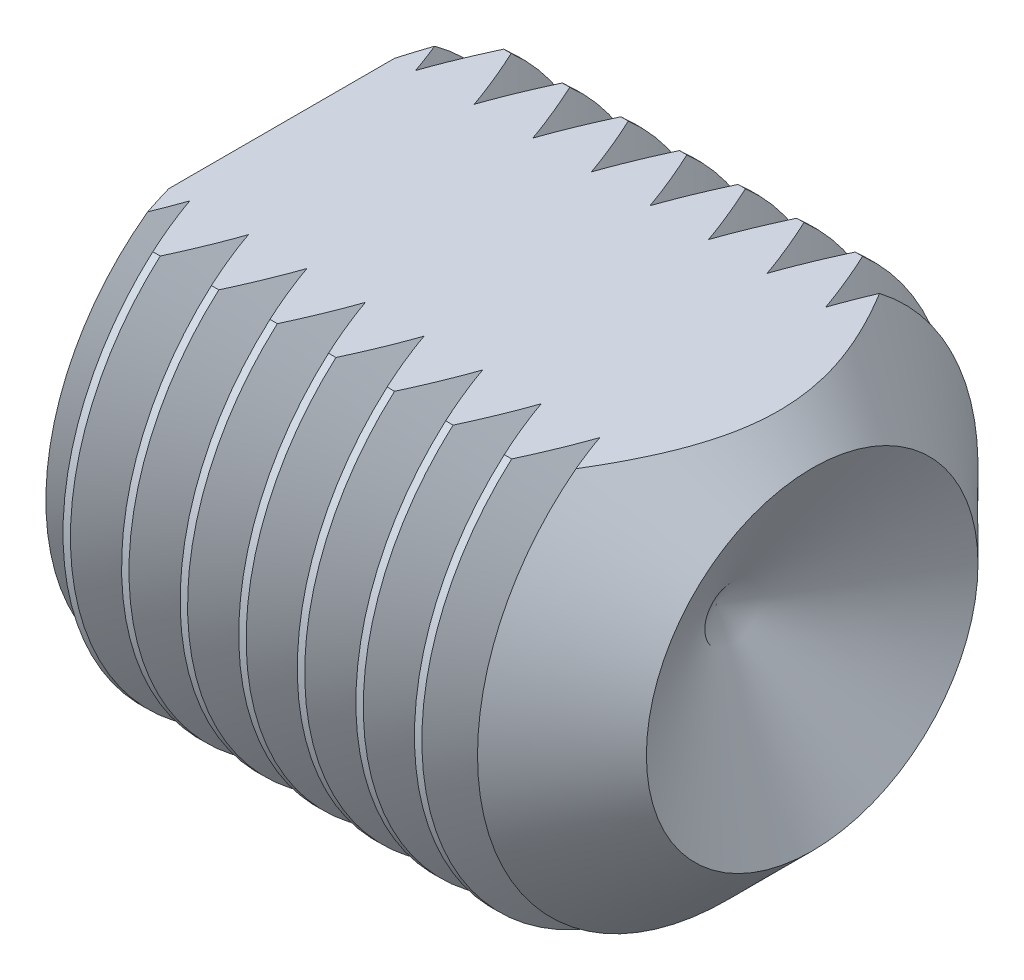
SolidWorks part; units mm, degrees
ref_plane "Plane1" through (0, 0, 0) normal (0, 0, 1) x (1, 0, 0)
ref_plane "Plane2" through (0, 0, 0) normal (0, 1, 0) x (1, 0, 0)
ref_plane "Plane3" through (0, 0, 0) normal (1, 0, 0) x (0, 0, -1)
sketch "BodySke" plane through (0, 0, 0) normal (0, 0, 1) x (1, 0, 0)
  line L0 (0, 0) -> (0, 6.8985)
  line L1 (0, 6.8985) -> (0.636, 8)
  line L2 (0.636, 8) -> (13, 8)
  line L3 (13, 8) -> (16, 5)
  line L4 (13.1132, 0) -> (0, 0)
  line L5 (-12.7, 0) -> (88.9, 0) construction
  line L6 (13.1132, 0) -> (16, 5)
  line L7 (16, 5) -> (16, 14.525) construction
  line L8 (0, -6.8985) -> (0.636, -8) construction
  line L9 (13.1132, 0) -> (16, -5) construction
  line L10 (13, -8) -> (16, -5) construction
  line L11 (1, 15.875) -> (1, -3.175) construction
  dimension "Length" = 16
  dimension "Diameter" = 16
  dimension "Drive_ch_ang" = 60
  dimension "Minor_dia" = 13.797
  dimension "Cup_nose_ang" = 45
  dimension "Cup_ang" = 120
  dimension "Cup_dia" = 10
  dimension "Advance" = 2
revolve "BaseBody" add sketch "BodySke" angle 360 about L5
cosmetic thread "ThreadCosmetic" [suppressed] parameters "Thread_minor"=13.797
sketch "Sketch2" plane through (0, 0, 0) normal (-1, 0, 0) x (0, 0, 1)
  line L0 (2.3094, 4) -> (-2.3094, 4)
  line L1 (-2.3094, 4) -> (-4.6188, 0)
  line L2 (2.3094, 4) -> (4.6188, 0)
  line L3 (2.3094, -4) -> (4.6188, 0)
  line L4 (2.3094, -4) -> (-2.3094, -4)
  line L5 (-2.3094, -4) -> (-4.6188, 0)
  dimension "Hex_size" = 8
  dimension "D2" = 4
  dimension "D3" = 4
extrude "Hex" cut sketch "Sketch2" against normal blind 6.4
sketch "ThdSchSke" plane through (0, 0, 0) normal (0, 0, 1) x (1, 0, 0)
  line L0 (0.636, -6.8985) -> (-0.1353, -8)
  line L1 (0.636, -6.8985) -> (1.4072, -8)
  line L2 (1.4072, -8) -> (1.4072, -10)
  line L3 (-3.175, 0) -> (5.1513, 0) construction
  line L4 (0.636, 8) -> (0.636, -8) construction
  line L5 (1.4072, -10) -> (-0.1353, -10)
  line L6 (-0.1353, -10) -> (-0.1353, -8)
  dimension "Thread_minor" = 13.797
  dimension "Diameter" = 16
  dimension "SideAngle" = 55
  dimension "VeeAngle" = 70
  dimension "Overcut" = 20
revolve "ThreadSchematic" cut sketch "ThdSchSke" angle 360 about L3
pattern_linear "ThdSchPat" count 8 spacing 1.7663 along (1, 0, 0) of "ThreadSchematic"
ref_plane "Plane4" through (0, 8, 0) normal (0, 1, 0) x (-1, 0, 0)
sketch "Sketch3" plane through (0, 8, 0) normal (0, 1, 0) x (-1, 0, 0)
  line L1 (-22.9785, -18.8446) -> (7.4421, -18.8446)
  line L2 (-22.9785, -18.8446) -> (-22.9785, 15.0069)
  line L3 (-22.9785, 15.0069) -> (7.4421, 15.0069)
  line L4 (7.4421, -18.8446) -> (7.4421, 15.0069)
extrude "Cut-Extrude1" cut sketch "Sketch3" against normal blind 2
equation "\"D2@Sketch2\" = \"Hex_size@Sketch2\" / 2"
equation "\"D3@Sketch2\" = \"Hex_size@Sketch2\" / 2"
equation "\"Thread_minor@ThreadCosmetic\" = \"Minor_dia@BodySke\""
equation "\"Thread_minor@ThdSchSke\" = \"Thread_minor@ThreadCosmetic\""
equation "\"Diameter@ThdSchSke\" = \"Diameter@BodySke\""
equation "\"Overcut@ThdSchSke\" = \"Diameter@BodySke\" * 1.25"
equation "\"Num_threads@ThdSchPat\" = int( (\"Length@BodySke\" - ( ( ( \"Diameter@BodySke\" - \"Minor_dia@BodySke\" ) * 0.5 ) / tan( \"Drive_ch_ang@BodySke\" * 0.017453292 ) ) - ( ( ( \"Diameter@BodySke\" - \"Cup_dia@BodySke\" ) * 0.5 ) * tan( \"Cup_nose_ang@BodySke\" * 0.017453292 ) ) ) / \"Advance@BodySke\" + 0.999 )  + 1"
equation "\"Advance@ThdSchPat\" = (\"Length@BodySke\" - ( ( ( \"Diameter@BodySke\" - \"Minor_dia@BodySke\" ) * 0.5 ) / tan( \"Drive_ch_ang@BodySke\" * 0.017453292 ) ) - ( ( ( \"Diameter@BodySke\" - \"Cup_dia@BodySke\" ) * 0.5 ) * tan( \"Cup_nose_ang@BodySke\" * 0.017453292 ) ) ) /  (\"Num_threads@ThdSchPat\" - 1) 'relax it"
equation "' \"Num_threads@ThdSchPat\" = \"Num_threads@ThdSchPat\" - sgn( \"Num_threads@ThdSchPat\" - 1) '---chamfered tips only---"
